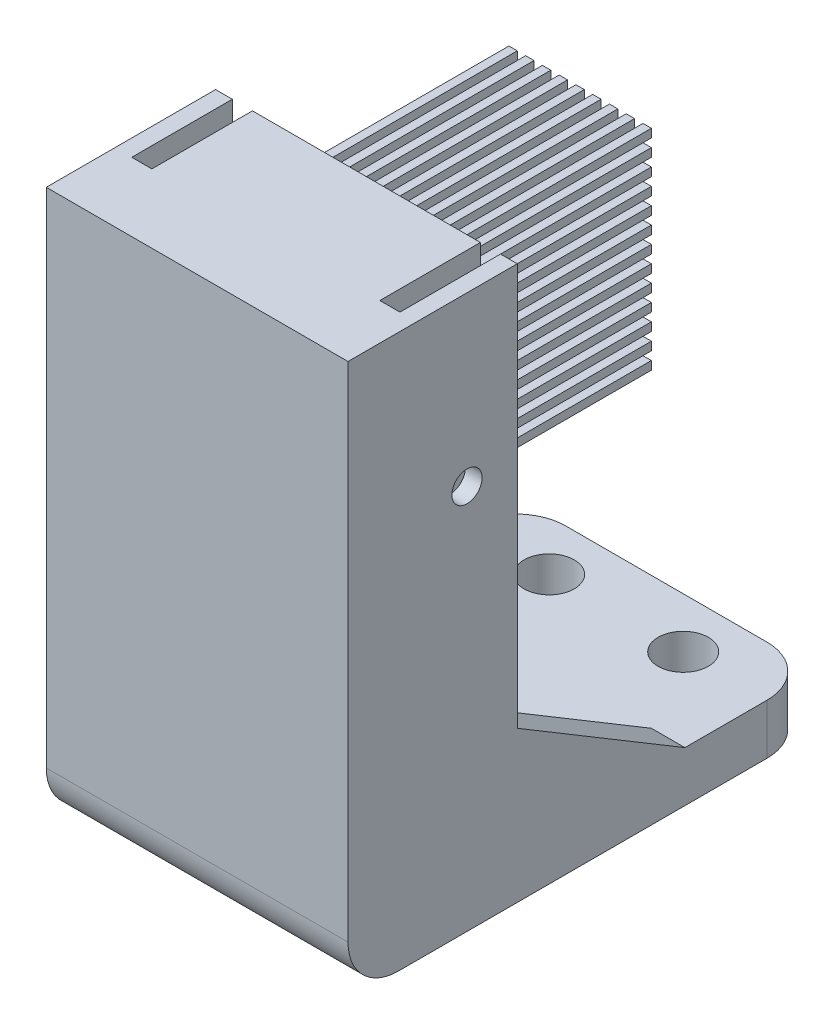
SolidWorks part; units mm, degrees
ref_plane "前视基准面" through (0, 0, 0) normal (0, 0, 1) x (1, 0, 0)
ref_plane "上视基准面" through (0, 0, 0) normal (0, 1, 0) x (1, 0, 0)
ref_plane "右视基准面" through (0, 0, 0) normal (1, 0, 0) x (0, 0, -1)
sketch "草图1" plane through (0, 0, 0) normal (0, 1, 0) x (1, 0, 0)
  line L0 (-57.4345, 0) -> (51.691, 0) construction
  line L1 (0, 59.2926) -> (0, -60.9819) construction
  line L2 (-9, 10.1) -> (-9, 0)
  line L3 (-9, 0) -> (9, 0)
  line L4 (9, 0) -> (9, 10.1)
  line L5 (9, 10.1) -> (4.5, 10.1)
  line L6 (-6, 8.1) -> (-6, 2)
  line L7 (-6, 2) -> (6, 2)
  line L8 (6, 2) -> (6, 8.1)
  line L9 (6, 8.1) -> (4.5, 8.1)
  line L10 (4.5, 8.1) -> (4.5, 10.1)
  line L11 (-6, 8.1) -> (-4.5, 8.1)
  line L12 (-4.5, 8.1) -> (-4.5, 10.1)
  line L13 (-4.5, 10.1) -> (-9, 10.1)
  dimension "D1" = 18
  dimension "D2" = 12
  dimension "D3" = 1.5
  dimension "D4" = 2
  dimension "D5" = 6.1
  dimension "D6" = 2
extrude "凸台-拉伸1" add sketch "草图1" along normal blind 30
sketch "草图2" plane through (0, 0, 0) normal (0, -1, 0) x (1, 0, 0)
  line L0 (9, 0) -> (-9, 0)
  line L1 (-9, 0) -> (-9, -28)
  line L2 (-9, -28) -> (9, -28)
  line L3 (9, -28) -> (9, 0)
  line L4 (0, -22.4608) -> (0, 12.6937) construction
  circle A0 centre (4, -25) radius 1.5
  circle A1 centre (-4, -25) radius 1.5
  dimension "D3" = 3
  dimension "D1" = 28
  dimension "D2" = 8
  dimension "D4" = 3
extrude "凸台-拉伸2" add sketch "草图2" along normal blind 3
sketch "草图3" plane through (0, 30, 0) normal (0, 1, 0) x (1, 0, 0)
  line L0 (-8, 10.1) -> (-6.8, 10.1)
  line L1 (-4.5, 10.1) -> (-9, 10.1) construction
  line L2 (-6.8, 10.1) -> (-6.8, 4.1)
  line L3 (-6.8, 4.1) -> (-8, 4.1)
  line L4 (-8, 4.1) -> (-8, 10.1)
  line L5 (-9, 10.1) -> (-9, 0) construction
  line L7 (0, 11.5268) -> (0, -2.7437) construction
  line L8 (8, 4.1) -> (8, 10.1)
  line L9 (6.8, 4.1) -> (8, 4.1)
  line L10 (6.8, 10.1) -> (6.8, 4.1)
  line L11 (8, 10.1) -> (6.8, 10.1)
  dimension "D1" = 1
  dimension "D2" = 1.2
  dimension "D3" = 6
extrude "切除-拉伸1" cut sketch "草图3" against normal blind 15
sketch "草图4" plane through (-9, 0, 0) normal (-1, 0, 0) x (0, 0, 1)
  line L1 (-10.1, 30) -> (-10.1, 0) construction
  line L2 (-10.1, 30) -> (0, 30) construction
  circle A0 centre (-7.1, 20) radius 0.9
  dimension "D1" = 1.8
  dimension "D2" = 3
  dimension "D3" = 10
extrude "切除-拉伸2" cut sketch "草图4" against normal up to surface (18 mm away) up to face at (9, 9, -12.7)
fillet "圆角1" radius 3 2 edges at (9, -1.5, -28) (-9, -1.5, -28)
sketch "草图5" plane through (-9, 0, 0) normal (-1, 0, 0) x (0, 0, 1)
  line L0 (-10.1, 0) -> (-10.1, 6)
  line L1 (-10.1, 30) -> (-10.1, 0) construction
  line L2 (-10.1, 6) -> (-20.1, 0)
  line L3 (-10.1, 0) -> (-25, 0) construction
  line L4 (-20.1, 0) -> (-10.1, 0)
  dimension "D1" = 10
  dimension "D2" = 6
extrude "凸台-拉伸3" add sketch "草图5" against normal blind 2
mirror "镜向1" about plane through (0, 0, 0) normal (1, 0, 0) of "凸台-拉伸3"
sketch "草图6" plane through (0, 0, 0) normal (0, 1, 0) x (1, 0, 0)
  line L0 (-6, 2) -> (6, 2)
  line L1 (6, 2) -> (6, 8.1)
  line L2 (6, 8.1) -> (4.5, 8.1)
  line L3 (-6, 8.1) -> (-6, 2)
  line L4 (-4.5, 8.1) -> (-4.5, 10.1)
  line L5 (-4.5, 10.1) -> (4.5, 10.1)
  line L6 (4.5, 10.1) -> (4.5, 8.1)
  line L7 (-4.5, 8.1) -> (-6, 8.1)
extrude "凸台-拉伸4" add sketch "草图6" along normal blind 5
fillet "圆角2" radius 3 1 edges at (0, -3, 0)
chamfer "倒角1" [suppressed] distance 0.5 angle 45
sketch "草图8" plane through (0, 30, 0) normal (0, 1, 0) x (1, 0, 0)
  line L0 (-6, 2) -> (6, 2)
  line L1 (6, 2) -> (6, 8.1)
  line L2 (6, 8.1) -> (4.5, 8.1)
  line L3 (4.5, 8.1) -> (4.5, 10.1)
  line L4 (4.5, 10.1) -> (-4.5, 10.1)
  line L5 (-4.5, 10.1) -> (-4.5, 8.1)
  line L6 (-4.5, 8.1) -> (-6, 8.1)
  line L7 (-6, 8.1) -> (-6, 2)
extrude "凸台-拉伸5" add sketch "草图8" against normal up to surface (25 mm away) up to face at (0, 5, -7.075)
sketch "草图9" plane through (0, 0, -10.1) normal (0, 0, -1) x (-1, 0, 0)
  line L0 (0, -19.7564) -> (0, 48.8792) construction
  line L1 (4.5, 15) -> (-4.5, 15)
  line L2 (-4.5, 15) -> (-4.5, 28)
  line L3 (-4.5, 28) -> (4.5, 28)
  line L4 (4.5, 28) -> (4.5, 15)
  line L5 (-6.8, 30) -> (6.8, 30) construction
  dimension "D1" = 9
  dimension "D2" = 2
  dimension "D3" = 13
extrude "凸台-拉伸6" add sketch "草图9" along normal blind 13
sketch "草图10" plane through (-9, 0, 0) normal (-1, 0, 0) x (0, 0, 1)
  circle A0 centre (-7.1, 20) radius 0.9
  dimension "D1" = 1.8
extrude "切除-拉伸3" cut sketch "草图10" against normal through all
shell "抽壳1" [suppressed] thickness 3
sketch "草图11" plane through (0, 0, -23.1) normal (0, 0, -1) x (-1, 0, 0)
  line L0 (4, 28) -> (3.5, 28)
  line L1 (4.5, 28) -> (-4.5, 28) construction
  line L2 (3.5, 28) -> (3.5, 27.5)
  line L3 (3.5, 27.5) -> (4, 27.5)
  line L5 (4, 27.5) -> (4, 28)
  line L6 (4.5, 15) -> (4.5, 28) construction
  line L7 (3, 28) -> (2.5, 28)
  line L8 (2.5, 28) -> (2.5, 27.5)
  line L9 (2.5, 27.5) -> (3, 27.5)
  line L10 (3, 27.5) -> (3, 28)
  line L11 (2, 28) -> (1.5, 28)
  line L12 (1.5, 28) -> (1.5, 27.5)
  line L13 (1.5, 27.5) -> (2, 27.5)
  line L14 (2, 27.5) -> (2, 28)
  line L15 (1, 28) -> (0.5, 28)
  line L16 (0.5, 28) -> (0.5, 27.5)
  line L17 (0.5, 27.5) -> (1, 27.5)
  line L18 (1, 27.5) -> (1, 28)
  line L19 (0, 28) -> (-0.5, 28)
  line L20 (-0.5, 28) -> (-0.5, 27.5)
  line L21 (-0.5, 27.5) -> (0, 27.5)
  line L22 (0, 27.5) -> (0, 28)
  line L23 (-1, 28) -> (-1.5, 28)
  line L24 (-1.5, 28) -> (-1.5, 27.5)
  line L25 (-1.5, 27.5) -> (-1, 27.5)
  line L26 (-1, 27.5) -> (-1, 28)
  line L27 (-2, 28) -> (-2.5, 28)
  line L28 (-2.5, 28) -> (-2.5, 27.5)
  line L29 (-2.5, 27.5) -> (-2, 27.5)
  line L30 (-2, 27.5) -> (-2, 28)
  line L31 (-3, 28) -> (-3.5, 28)
  line L32 (-3.5, 28) -> (-3.5, 27.5)
  line L33 (-3.5, 27.5) -> (-3, 27.5)
  line L34 (-3, 27.5) -> (-3, 28)
  line L35 (-4, 28) -> (-4.5, 28)
  line L36 (-4.5, 28) -> (-4.5, 27.5)
  line L37 (-4.5, 27.5) -> (-4, 27.5)
  line L38 (-4, 27.5) -> (-4, 28)
  dimension "D1" = 0.5
  dimension "D2" = 0.5
  dimension "D3" = 0.5
  dimension "D4" = 9
extrude "切除-拉伸4" cut sketch "草图11" against normal blind 13
sketch "草图12" plane through (0, 0, -23.1) normal (0, 0, -1) x (-1, 0, 0)
  line L0 (4.5, 27.5) -> (4.5, 27)
  line L1 (4.5, 15) -> (4.5, 28) construction
  line L2 (4.5, 27) -> (-4.5, 27)
  line L3 (-4.5, 27) -> (-4.5, 27.5)
  line L4 (-4.5, 27.5) -> (4.5, 27.5)
  line L5 (-4.5, 27.5) -> (-4.5, 15) construction
  dimension "D1" = 0.5
extrude "切除-拉伸5" cut sketch "草图12" against normal blind 13
pattern_linear "阵列(线性)1" count 13 spacing 1 along (0, -1, 0) of "切除-拉伸4", "切除-拉伸5"
